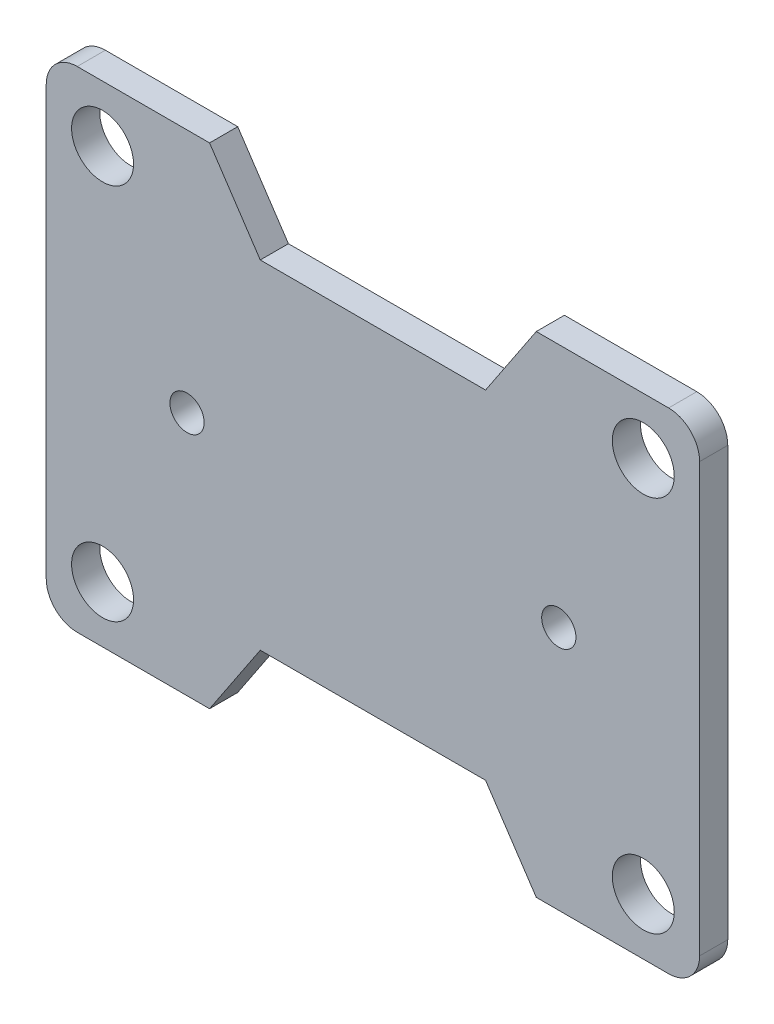
SolidWorks part; units mm, degrees
ref_plane "前视基准面" through (0, 0, 0) normal (0, 0, 1) x (1, 0, 0)
ref_plane "上视基准面" through (0, 0, 0) normal (0, 1, 0) x (1, 0, 0)
ref_plane "右视基准面" through (0, 0, 0) normal (1, 0, 0) x (0, 0, -1)
sketch "Sketch1" plane through (0, 0, 0) normal (0, 0, 1) x (1, 0, 0)
  line L0 (0, 33.5) -> (0, 36.25)
  line L1 (0, 0) -> (48, 0)
  line L2 (0, 0) -> (0, 33.5)
  line L3 (0, 33.5) -> (48, 33.5)
  line L4 (48, 0) -> (48, 33.5)
  line L5 (48, 33.5) -> (48, 36.25)
  line L6 (0, 0) -> (0, -2.75)
  line L7 (0, 2.75) -> (0, 30.75)
  line L8 (48, 0) -> (48, -2.75)
  line L9 (0, 16.75) -> (48, 16.75)
  line L10 (40.5, 16.75) -> (40.5, 18.27)
  line L11 (40.5, 16.75) -> (7.5, 16.75)
  line L12 (7.5, 16.75) -> (7.5, 18.27)
  line L13 (24, 16.75) -> (7.5, 16.75)
  line L14 (24, 16.75) -> (40.5, 16.75)
  line L15 (24, 33.5) -> (24, 38.5)
  line L16 (0, 16.75) -> (-5, 16.75)
  line L17 (-5, 16.75) -> (-5, 38.5)
  line L18 (-5, 38.5) -> (24, 38.5)
  line L19 (48, 16.75) -> (53, 16.75)
  line L20 (24, 0) -> (24, -5)
  line L21 (24, -5) -> (-5, -5)
  line L22 (-5, -5) -> (-5, 16.75)
  line L23 (24, -5) -> (53, -5)
  line L24 (53, -5) -> (53, 16.75)
  line L25 (53, 16.75) -> (53, 38.5)
  line L26 (53, 38.5) -> (24, 38.5)
  line L27 (24, 16.75) -> (24, 31.75)
  line L28 (24, 16.75) -> (24, 1.75)
  line L29 (24, 1.75) -> (14, 1.75)
  line L30 (14, 1.75) -> (24, 1.75)
  line L31 (24, 1.75) -> (34, 1.75)
  line L32 (24, 31.75) -> (14, 31.75)
  line L33 (14, 31.75) -> (34, 31.75)
  line L34 (34, 31.75) -> (38.5, 38.5)
  line L35 (38.5, 38.5) -> (9.5, 38.5)
  line L36 (9.5, 38.5) -> (14, 31.75)
  line L37 (9.5, -5) -> (14, 1.75)
  line L38 (34, 1.75) -> (38.5, -5)
  line L39 (38.5, -5) -> (9.5, -5)
  circle A0 centre (0, 33.5) radius 2.75
  circle A1 centre (48, 33.5) radius 2.75
  circle A2 centre (0, 0) radius 2.75
  circle A3 centre (48, 0) radius 2.75
  circle A4 centre (40.5, 16.75) radius 1.52
  circle A5 centre (7.5, 16.75) radius 1.52
  dimension "D1" = 2.75
  dimension "D2" = 48
  dimension "D3" = 2.75
  dimension "D4" = 2.75
  dimension "D5" = 28
  dimension "D6" = 2.75
  dimension "D7" = 1.52
  dimension "D8" = 1.52
  dimension "D9" = 16.5
  dimension "D10" = 16.5
  dimension "D11" = 5
  dimension "D12" = 5
  dimension "D13" = 5
  dimension "D14" = 5
  dimension "D15" = 15
  dimension "D16" = 15
  dimension "D17" = 10
  dimension "D18" = 10
extrude "Boss-Extrude1" add sketch "Sketch1" along normal blind 2.5 contours A5 L16 L22 L21 L37 L1 A2 L2 | A5 L2 A0 L3 L36 L18 L17 L16 | A5 L13 L27 L32 L36 L3 A0 L2 | A4 L4 A1 L3 L34 L33 L27 L11 | A4 L19 L25 L26 L34 L3 A1 L4 | A4 L4 A3 L1 L38 L23 L24 L19 | A4 L11 L28 L31 L38 L1 A3 L4 | A5 L2 A2 L1 L37 L29 L28 L13
fillet "Fillet1" radius 2.75 4 edges at (53, 38.5, 1.25) (53, -5, 1.25) (-5, -5, 1.25) (-5, 38.5, 1.25)
